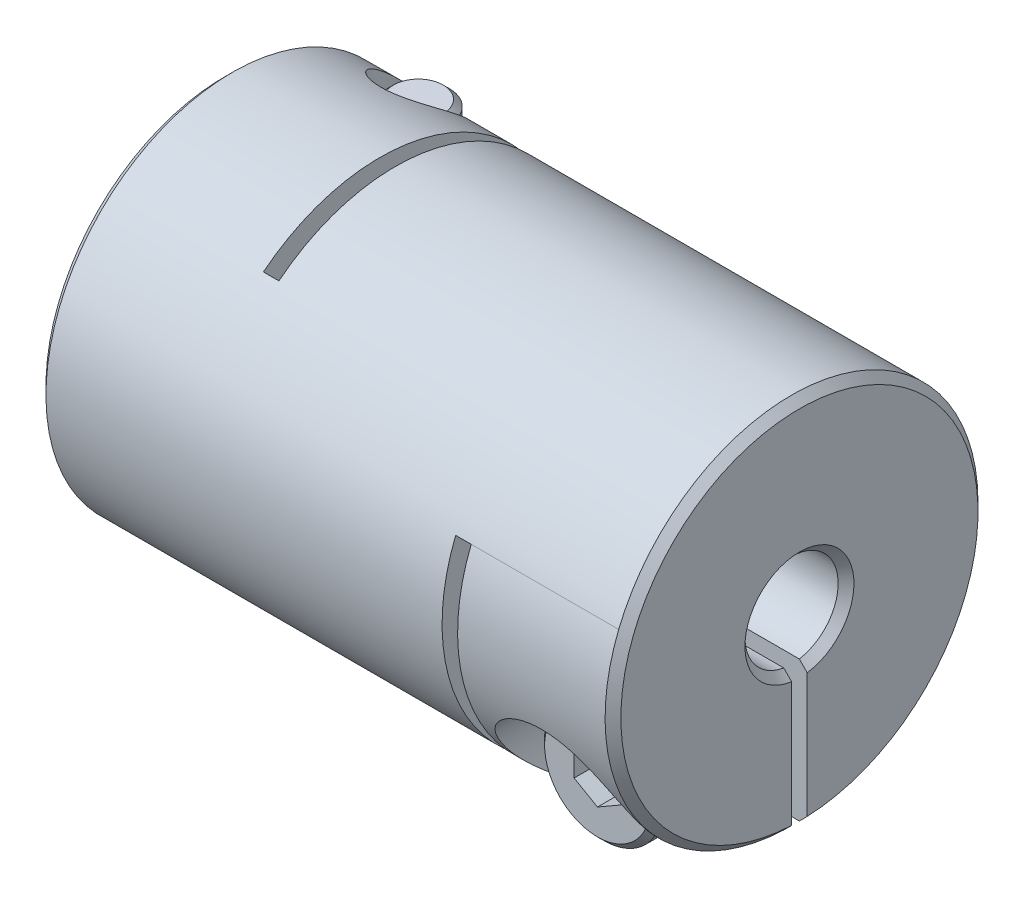
SolidWorks part; units mm, degrees
ref_plane "Front Plane" through (0, 0, 0) normal (0, 0, 1) x (1, 0, 0)
ref_plane "Top Plane" through (0, 0, 0) normal (0, 1, 0) x (1, 0, 0)
ref_plane "Right Plane" through (0, 0, 0) normal (1, 0, 0) x (0, 0, -1)
sketch "Sketch1" plane through (0, 0, 0) normal (1, 0, 0) x (0, 0, -1)
  circle A0 centre (0, 0) radius 6
  dimension "dim D" = 12
extrude "Boss-Extrude1" add sketch "Sketch1" along normal mid plane 18.5
sketch "Sketch2" plane through (9.25, 0, 0) normal (1, 0, 0) x (0, 0, -1)
  circle A0 centre (0, 0) radius 1.5
  dimension "dim D1" = 3
extrude "Cut-Extrude1" cut sketch "Sketch2" against normal through all
chamfer "Chamfer1" distance 0.254 angle 45 4 edges at (-9.25, 0, -1.5) (-9.25, 0, -6) (9.25, 0, -6) (9.25, 0, -1.5)
ref_plane "Plane2" through (0, -6, 0) normal (0, -1, 0) x (1, 0, 0)
ref_plane "L1" through (-6.75, 0, 0) normal (-1, 0, 0) x (0, 0, 1)
sketch "Sketch4" plane through (0, -6, 0) normal (0, -1, 0) x (1, 0, 0)
  line L0 (-8.996, -6) -> (8.996, -6) construction
  line L1 (-4.25, -6) -> (-3.75, -6)
  line L2 (-4.25, -6) -> (-4.25, 3.75)
  line L3 (-4.25, 3.75) -> (-3.75, 3.75)
  line L4 (-3.75, -6) -> (-3.75, 3.75)
  line L5 (-4.25, 1.5) -> (-4.25, 6) construction
  line L6 (8.996, 1.5) -> (-8.996, 1.5) construction
  line L7 (8.996, 6) -> (-8.996, 6) construction
  line L10 (-4.25, 3.75) -> (-9.25, 3.75) construction
  line L11 (-9.25, 5.746) -> (-9.25, -5.746) construction
  line L12 (-6.75, 10.2256) -> (-6.75, -10.2256) construction
  point P16 (-6.75, 3.75)
  dimension "D1" = 0.5
extrude "Cut-Extrude2" cut sketch "Sketch4" against normal through all
ref_plane "Plane4" through (0, 0, -6) normal (0, 0, -1) x (-1, 0, 0)
sketch "Sketch7" plane through (0, 0, -6) normal (0, 0, -1) x (-1, 0, 0)
  line L1 (-3.75, -6) -> (-4.25, -6)
  line L2 (-4.25, -6) -> (-4.25, 2.25)
  line L3 (-4.25, 2.25) -> (-3.75, 2.25)
  line L4 (-3.75, -6) -> (-3.75, 2.25)
  line L5 (9.25, 8.6487) -> (6.75, 8.6487) construction
  line L7 (-10.505, -6) -> (10.505, -6) construction
  line L8 (-8.996, -1.5) -> (3.75, -1.5) construction
  line L9 (9.25, -5.746) -> (9.25, 5.746) construction
  line L10 (-8.996, -1.5) -> (3.75, -1.5) construction
  line L11 (3.75, 4.6837) -> (4.25, 4.6837) construction
  line L12 (-4.25, 2.25) -> (-4.25, -6) construction
  line L14 (-8.996, -1.5) -> (3.75, -1.5) construction
  line L16 (-8.996, -1.5) -> (3.75, -1.5) construction
  line L17 (4.25, -6) -> (8.996, -6) construction
  line L18 (6.75, -10.2256) -> (6.75, 10.2256) construction
  line L19 (-8.996, -6) -> (-8.996, 6) construction
  line L20 (-9.25, 2.25) -> (-6.75, 2.25) construction
  line L21 (-9.25, 5.746) -> (-9.25, -5.746) construction
  line L22 (-6.75, 2.25) -> (-4.25, 2.25) construction
  line L23 (-8.996, -6) -> (-8.996, 6) construction
  line L24 (-8.996, -1.5) -> (-8.996, 6) construction
  line L25 (-8.996, -1.5) -> (3.75, -1.5) construction
  point P23 (-4.25, 2.25)
  point P33 (-8.996, 2.25)
extrude "Cut-Extrude3" cut sketch "Sketch7" against normal through all
sketch "Sketch8" plane through (0, 0, 0) normal (0, 1, 0) x (1, 0, 0)
  line L0 (-4.25, -3.75) -> (-4.25, 6) construction
  line L1 (-9.25, 6) -> (-4.25, 6)
  line L2 (-9.25, 6) -> (-9.25, 0)
  line L3 (-9.25, 0) -> (-4.25, 0)
  line L4 (-4.25, 6) -> (-4.25, 0)
  line L5 (10.505, 6) -> (-10.505, 6) construction
  line L6 (-9.25, 5.746) -> (-9.25, -5.746) construction
extrude "Cut-Extrude5" cut sketch "Sketch8" against normal mid plane 0.5
sketch "Sketch13" plane through (0, 0, 0) normal (0, 0, 1) x (1, 0, 0)
  line L0 (9.25, -5.746) -> (9.25, 5.746) construction
  line L1 (4.25, -6) -> (9.25, -6)
  line L2 (4.25, -6) -> (4.25, 0)
  line L3 (4.25, 0) -> (9.25, 0)
  line L4 (9.25, -6) -> (9.25, 0)
extrude "Cut-Extrude6" cut sketch "Sketch13" against normal mid plane 0.5
hole_wizard "CBORE for M2 SHCS1" positions "Sketch12" profile "Sketch11" counterbore size "M2" standard "Ansi Metric" end condition through all
sketch "Sketch12" plane through (0, -6, 0) normal (0, -1, 0) x (1, 0, 0)
  line L0 (-6.75, 10.2256) -> (-6.75, -10.2256) construction
  line L1 (-4.25, -1.479) -> (-4.25, -5.9948) construction
  line L2 (-4.25, -1.479) -> (-4.25, -5.9948)
  line L3 (-4.25, -3.7369) -> (-6.75, -3.7369) construction
  point P0 (-6.75, -3.7369)
sketch "Sketch11" plane through (-6.75, -6, -3.7369) normal (1, 0, 0) x (0, 0, -1)
  line L0 (0, 0) -> (0, 12)
  line L1 (0, 12) -> (1.2, 12)
  line L3 (1.2, 12) -> (1.2, 4)
  line L4 (1.2, 4) -> (2.2, 4)
  line L5 (2.2, 4) -> (2.2, 0)
  line L7 (2.2, 0) -> (0, 0)
  line L11 (0, -6.35) -> (0, 107.95) construction
  dimension "Thru Hole Dia." = 2.4
  dimension "Thru Hole Depth" = 12
  dimension "C'Bore Dia." = 4.4
  dimension "C'Bore Depth" = 4
ref_plane "Plane5" through (0, 0, 6) normal (0, 0, 1) x (1, 0, 0)
hole_wizard "CBORE for M2 SHCS2" positions "Sketch15" profile "Sketch14" counterbore size "M2" standard "Ansi Metric" end condition through all
sketch "Sketch15" plane through (0, 0, 6) normal (0, 0, 1) x (1, 0, 0)
  line L0 (-8.95, -2) -> (-4.55, -2) construction
  line L1 (-8.95, -2) -> (-4.55, -2)
  line L5 (0, 0) -> (0, 6) construction
  line L6 (-4.25, 6) -> (-8.996, 6) construction
  line L8 (8.95, -2) -> (4.55, -2)
  line L9 (6.75, -2) -> (6.75, -3.7369) construction
  line L11 (6.75, -5.9948) -> (6.75, -1.479) construction
  line L12 (8.996, -5.9948) -> (4.25, -5.9948) construction
  line L13 (4.25, -1.479) -> (8.996, -1.479) construction
  point P0 (6.75, -3.7369)
sketch "Sketch14" plane through (6.75, -3.7369, 6) normal (1, 0, 0) x (0, -1, 0)
  line L0 (0, 0) -> (0, 12)
  line L1 (0, 12) -> (1.2, 12)
  line L3 (1.2, 12) -> (1.2, 4)
  line L4 (1.2, 4) -> (2.2, 4)
  line L5 (2.2, 4) -> (2.2, 0)
  line L7 (2.2, 0) -> (0, 0)
  line L11 (0, -6.35) -> (0, 107.95) construction
  dimension "Thru Hole Dia." = 2.4
  dimension "Thru Hole Depth" = 12
  dimension "C'Bore Dia." = 4.4
  dimension "C'Bore Depth" = 4
sketch "Sketch16" plane through (0, 0, 2) normal (0, 0, 1) x (1, 0, 0)
  circle A0 centre (6.75, -3.7369) radius 1.9
  dimension "screw dia" = 3.8
extrude "Boss-Extrude2" add sketch "Sketch16" along normal blind 2 separate body
sketch "Sketch17" plane through (0, 0, 2) normal (0, 0, -1) x (-1, 0, 0)
  circle A0 centre (-6.75, -3.7369) radius 1
  dimension "D1" = 2
extrude "Boss-Extrude3" add sketch "Sketch17" along normal blind 6.5
chamfer "Chamfer2" distance 0.2 angle 45 3 edges at (5.75, -3.7369, -4.5) (8.65, -3.7369, 2) (8.65, -3.7369, 4)
sketch "Sketch18" plane through (0, 0, 4) normal (0, 0, 1) x (1, 0, 0)
  line L1 (6.75, -4.6029) -> (7.5, -4.1699)
  line L2 (7.5, -4.1699) -> (7.5, -3.3039)
  line L3 (7.5, -3.3039) -> (6.75, -2.8709)
  line L4 (6.75, -2.8709) -> (6, -3.3039)
  line L5 (6, -3.3039) -> (6, -4.1699)
  line L6 (6, -4.1699) -> (6.75, -4.6029)
  circle A0 centre (6.75, -3.7369) radius 0.75 construction
  dimension "hex" = 1.5
extrude "Cut-Extrude7" cut sketch "Sketch18" against normal blind 1.5
mirror "Mirror1" about plane through (0, 0, 0) normal (1, 0, 0) of bodies 121
pattern_circular "CirPattern1" count 2 every 90 about axis through (0, 0, 0) along (1, 0, 0) of bodies 122
delete or keep bodies "Body-Delete1" type delete bodies bodies 122
